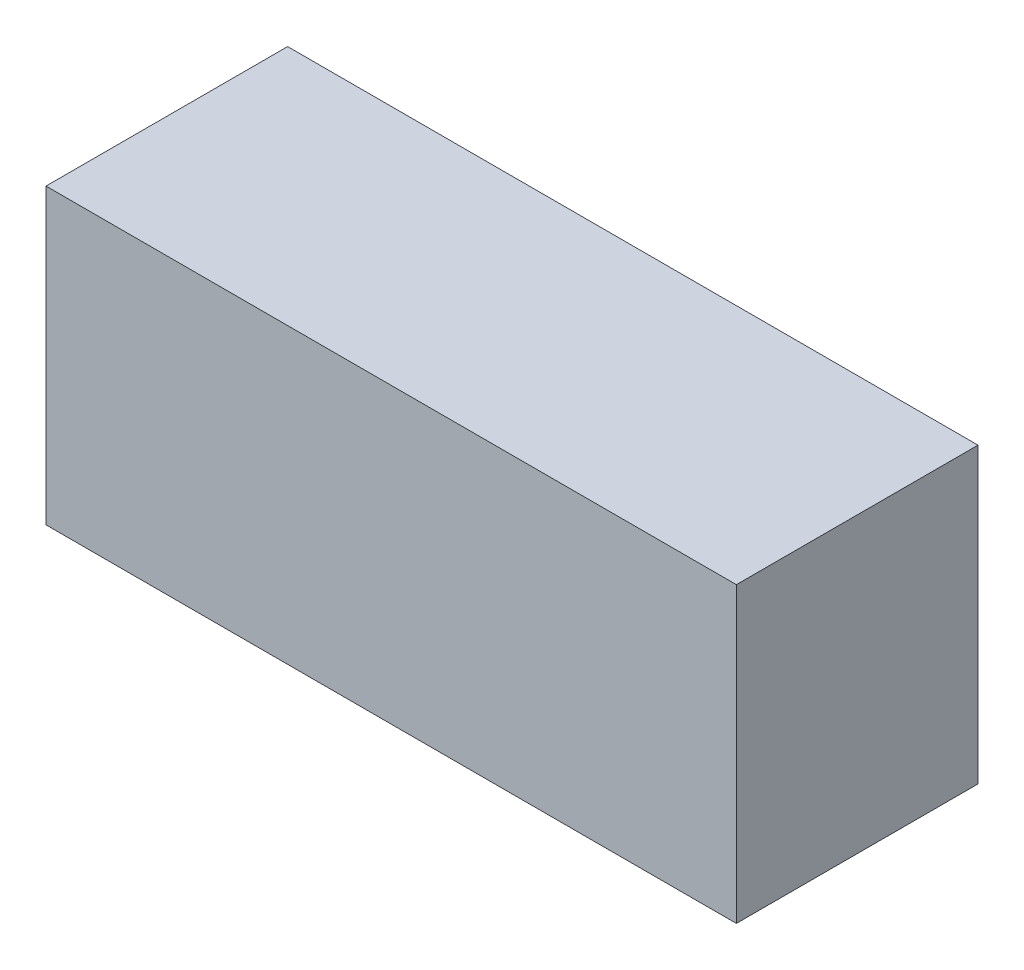
SolidWorks part; units mm, degrees
ref_plane "前视基准面" through (0, 0, 0) normal (0, 0, 1) x (1, 0, 0)
ref_plane "上视基准面" through (0, 0, 0) normal (0, 1, 0) x (1, 0, 0)
ref_plane "右视基准面" through (0, 0, 0) normal (1, 0, 0) x (0, 0, -1)
sketch "草图1" plane through (0, 0, 0) normal (0, 0, 1) x (1, 0, 0)
  line L1 (0, 0) -> (400, 0)
  line L2 (0, 0) -> (0, 170)
  line L3 (0, 170) -> (400, 170)
  line L4 (400, 0) -> (400, 170)
  dimension "D1" = 170
  dimension "D2" = 400
extrude "凸台-拉伸1" add sketch "草图1" along normal blind 140
